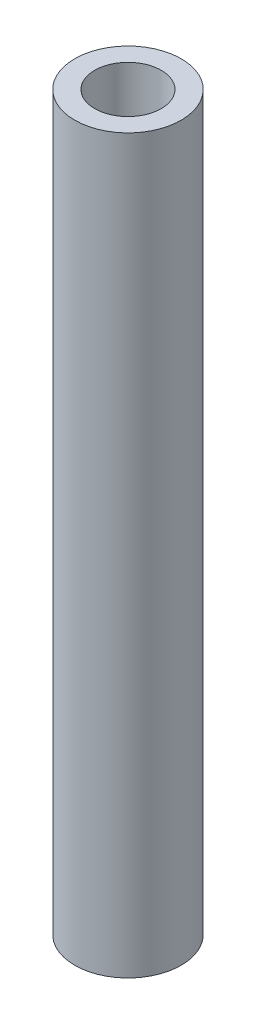
SolidWorks part; units mm, degrees
material "1060 Alloy"
ref_plane "Front Plane" through (0, 0, 0) normal (0, 0, 1) x (1, 0, 0)
ref_plane "Top Plane" through (0, 0, 0) normal (0, 1, 0) x (1, 0, 0)
ref_plane "Right Plane" through (0, 0, 0) normal (1, 0, 0) x (0, 0, -1)
sketch "Sketch1" plane through (0, 0, 0) normal (0, 1, 0) x (1, 0, 0)
  circle A0 centre (0, 0) radius 4
  circle A1 centre (0, 0) radius 2.5
  dimension "D1" = 8
  dimension "D2" = 5
extrude "Boss-Extrude1" add sketch "Sketch1" along normal blind 55
